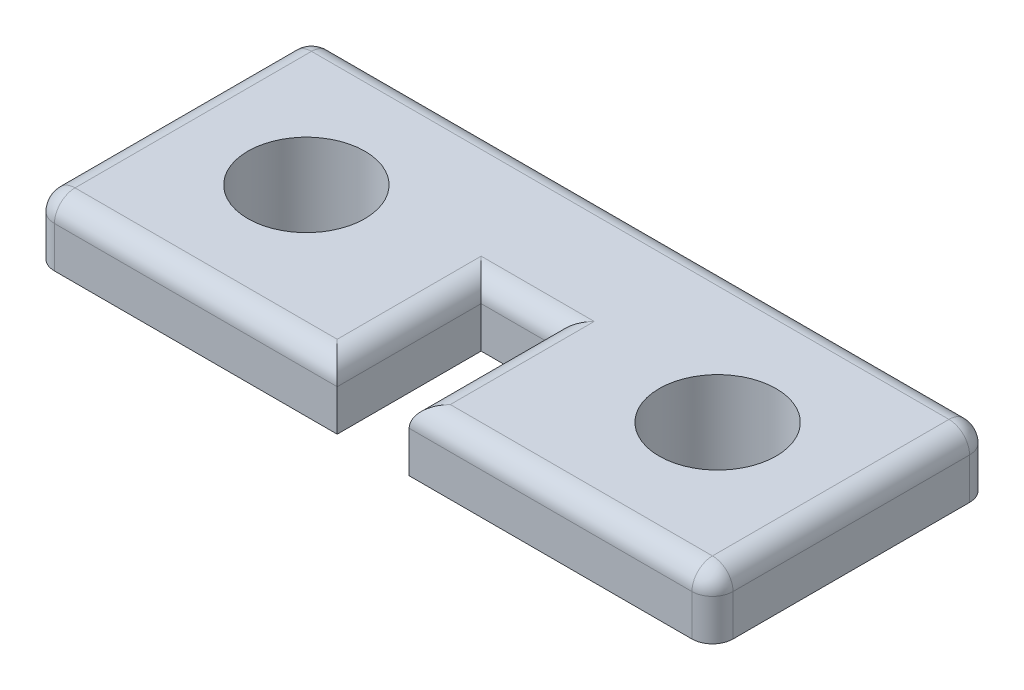
SolidWorks part; units mm, degrees
material "EPDM 60 Durometer"
ref_plane "Front Plane" through (0, 0, 0) normal (0, 0, 1) x (1, 0, 0)
ref_plane "Top Plane" through (0, 0, 0) normal (0, 1, 0) x (1, 0, 0)
ref_plane "Right Plane" through (0, 0, 0) normal (1, 0, 0) x (0, 0, -1)
sketch "Sketch1" plane through (0, 0, 0) normal (0, 1, 0) x (1, 0, 0)
  line L0 (-5, 0) -> (5, 0) construction
  line L1 (-8.25, -3.375) -> (8.25, -3.375) construction
  line L2 (-8.25, -3.375) -> (-8.25, 3.375)
  line L3 (-8.25, 3.375) -> (8.25, 3.375)
  line L4 (8.25, -3.375) -> (8.25, 3.375)
  line L5 (-8.25, -3.375) -> (8.25, 3.375) construction
  line L6 (-8.25, 3.375) -> (8.25, -3.375) construction
  line L7 (0, 0) -> (0, -3.375) construction
  line L8 (-0.875, -3.375) -> (-8.25, -3.375)
  line L9 (0.875, 0.125) -> (-0.875, 0.125)
  line L10 (0.875, 0.125) -> (0.875, -3.375)
  line L11 (0.875, -3.375) -> (-0.875, -3.375) construction
  line L12 (-0.875, 0.125) -> (-0.875, -3.375)
  line L13 (0.875, 0.125) -> (-0.875, -3.375) construction
  line L14 (0.875, -3.375) -> (-0.875, 0.125) construction
  line L15 (0.875, -3.375) -> (8.25, -3.375)
  circle A0 centre (-5, 0) radius 1.4225
  circle A1 centre (5, 0) radius 1.4225
  point P0 (0, 0)
  point P9 (0, 0)
  point P13 (0, -1.625)
  dimension "D4" = 2.845
  dimension "D1" = 16.5
  dimension "D2" = 6.75
  dimension "D3" = 10
  dimension "D5" = 1.75
  dimension "D6" = 3.5
extrude "Boss-Extrude1" add sketch "Sketch1" along normal blind 1.5
sketch "Sketch2" plane through (0, 0, 0) normal (0, -1, 0) x (1, 0, 0)
  circle A0 centre (5, 0) radius 1.4225 construction
  circle A1 centre (5, 0) radius 1.4225
  circle A2 centre (-5, 0) radius 1.4225 construction
  circle A3 centre (-5, 0) radius 1.4225
  circle A4 centre (5, 0) radius 2.0225
  circle A5 centre (-5, 0) radius 2.0225
  dimension "D1" = 0.6
  dimension "D2" = 0.6
extrude "Boss-Extrude2" add sketch "Sketch2" along normal blind 1.5
fillet "Fillet1" radius 0.5 2 edges at (-5, -1.5, -2.0225) (5, -1.5, -2.0225)
fillet "Fillet2" radius 0.5 12 edges at (8.25, 0.75, 3.375) (8.25, 0.75, -3.375) (-8.25, 0.75, 3.375) (-8.25, 0.75, -3.375) (0, 1.5, -3.375) (8.25, 1.5, 0) (4.5625, 1.5, 3.375) (0.875, 1.5, 1.625) (0, 1.5, -0.125) (-0.875, 1.5, 1.625) (-4.5625, 1.5, 3.375) (-8.25, 1.5, 0)
equation "\"D2@Sketch2\"=\"D1@Sketch2\""
